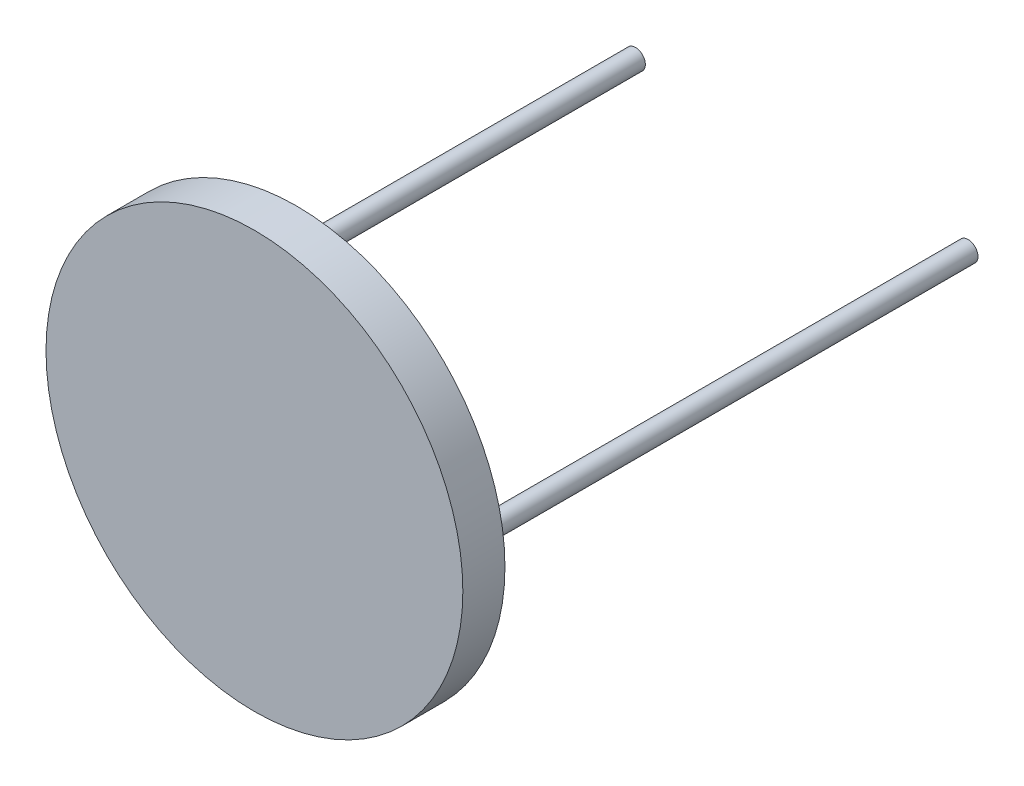
SolidWorks part; units mm, degrees
ref_plane "Front" through (0, 0, 0) normal (0, 0, 1) x (1, 0, 0)
ref_plane "Top" through (0, 0, 0) normal (0, 1, 0) x (1, 0, 0)
ref_plane "Right" through (0, 0, 0) normal (1, 0, 0) x (0, 0, -1)
sketch "Sketch1" plane through (0, 0, 0) normal (0, 0, 1) x (1, 0, 0)
  circle A0 centre (0, 0) radius 9.9
  dimension "D1" = 19.8
extrude "Boss-Extrude1" add sketch "Sketch1" along normal blind 2
sketch "Sketch2" plane through (0, 0, 0) normal (0, 0, -1) x (-1, 0, 0)
  circle A0 centre (-7.9, 0) radius 0.47
  circle A1 centre (7.9, 0) radius 0.47
  dimension "D1" = 0.94
  dimension "D2" = 0.94
  dimension "D3" = 15.8
  dimension "D4" = 7.9
extrude "Boss-Extrude2" add sketch "Sketch2" along normal blind 24
equation "\"D4@Sketch2\"=\"D3@Sketch2\"/2"
